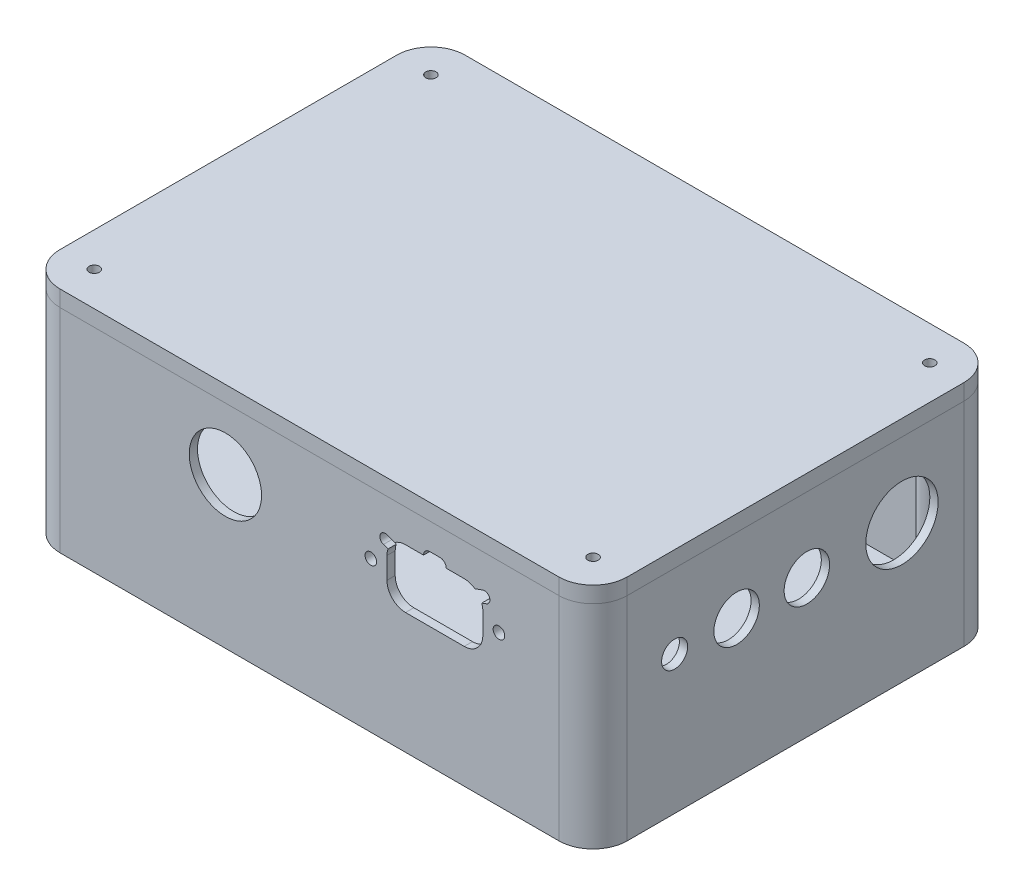
SolidWorks part; units mm, degrees
material "ABS"
ref_plane "Front Plane" through (0, 0, 0) normal (0, 0, 1) x (1, 0, 0)
ref_plane "Top Plane" through (0, 0, 0) normal (0, 1, 0) x (1, 0, 0)
ref_plane "Right Plane" through (0, 0, 0) normal (1, 0, 0) x (0, 0, -1)
sketch "Sketch1" plane through (0, 0, 0) normal (0, 1, 0) x (1, 0, 0)
  line L0 (-76.6347, 59.69) -> (76.6347, 59.69)
  line L1 (-76.6347, 62.23) -> (76.6347, 62.23)
  line L2 (-87.1347, 51.73) -> (-87.1347, -51.73)
  line L3 (-76.6347, -62.23) -> (76.6347, -62.23)
  line L4 (87.1347, 51.73) -> (87.1347, -51.73)
  line L5 (-87.1347, 62.23) -> (87.1347, -62.23) construction
  line L6 (-87.1347, -62.23) -> (87.1347, 62.23) construction
  line L7 (84.5947, 51.73) -> (84.5947, -51.73)
  line L8 (-76.6347, -59.69) -> (76.6347, -59.69)
  line L9 (-84.5947, 51.73) -> (-84.5947, -51.73)
  arc A0 (-87.1347, -51.73) -> (-76.6347, -62.23) centre (-76.6347, -51.73) ccw
  arc A1 (76.6347, -62.23) -> (87.1347, -51.73) centre (76.6347, -51.73) ccw
  arc A2 (76.6347, 62.23) -> (87.1347, 51.73) centre (76.6347, 51.73) cw
  arc A3 (-76.6347, 62.23) -> (-87.1347, 51.73) centre (-76.6347, 51.73) ccw
  arc A4 (76.6347, 59.69) -> (84.5947, 51.73) centre (76.6347, 51.73) cw
  arc A5 (76.6347, -59.69) -> (84.5947, -51.73) centre (76.6347, -51.73) ccw
  arc A6 (-84.5947, -51.73) -> (-76.6347, -59.69) centre (-76.6347, -51.73) ccw
  arc A7 (-76.6347, 59.69) -> (-84.5947, 51.73) centre (-76.6347, 51.73) ccw
  circle A8 centre (-76.6347, 51.73) radius 1.5875
  circle A9 centre (-76.6347, 51.73) radius 2.9845
  circle A10 centre (76.6347, 51.73) radius 1.5875
  circle A11 centre (76.6347, 51.73) radius 2.9845
  circle A12 centre (76.6347, -51.73) radius 1.5875
  circle A13 centre (76.6347, -51.73) radius 2.9845
  circle A14 centre (-76.6347, -51.73) radius 1.5875
  circle A15 centre (-76.6347, -51.73) radius 2.9845
  point P0 (0, 0)
  dimension "D3" = 10.5
  dimension "D5" = 5.969
  dimension "D6" = 3.175
  dimension "D1" = 124.46
  dimension "D2" = 174.2694
  dimension "D4" = 2.54
extrude "Sides" add sketch "Sketch1" along normal blind 60.96 contours L1 A3 L2 A0 L3 A1 L4 A2 A7 L0 A4 L7 A5 L8 A6 L9 | A9 A8 | A11 A10 | A13 A12 | A15 A14
sketch "Sketch2" plane through (0, 0, 0) normal (0, 1, 0) x (1, 0, 0)
  line L4 (-76.6347, -62.23) -> (76.6347, -62.23) construction
  line L5 (87.1347, 51.73) -> (87.1347, -51.73) construction
  line L6 (-76.6347, 62.23) -> (76.6347, 62.23) construction
  line L7 (-87.1347, 51.73) -> (-87.1347, -51.73) construction
  line L8 (-76.6347, -62.23) -> (76.6347, -62.23)
  line L9 (87.1347, 51.73) -> (87.1347, -51.73)
  line L10 (-76.6347, 62.23) -> (76.6347, 62.23)
  line L11 (-87.1347, 51.73) -> (-87.1347, -51.73)
  arc A4 (-87.1347, -51.73) -> (-76.6347, -62.23) centre (-76.6347, -51.73) ccw construction
  arc A5 (76.6347, -62.23) -> (87.1347, -51.73) centre (76.6347, -51.73) ccw construction
  arc A6 (87.1347, 51.73) -> (76.6347, 62.23) centre (76.6347, 51.73) ccw construction
  arc A7 (-76.6347, 62.23) -> (-87.1347, 51.73) centre (-76.6347, 51.73) ccw construction
  arc A8 (-87.1347, -51.73) -> (-76.6347, -62.23) centre (-76.6347, -51.73) ccw
  arc A9 (76.6347, -62.23) -> (87.1347, -51.73) centre (76.6347, -51.73) ccw
  arc A10 (87.1347, 51.73) -> (76.6347, 62.23) centre (76.6347, 51.73) ccw
  arc A11 (-76.6347, 62.23) -> (-87.1347, 51.73) centre (-76.6347, 51.73) ccw
extrude "Bottom" add sketch "Sketch2" against normal blind 4.318
sketch "Sketch3" plane through (0, 60.96, 0) normal (0, 1, 0) x (1, 0, 0)
  line L0 (-87.1347, 51.73) -> (-87.1347, -51.73) construction
  line L1 (-76.6347, 62.23) -> (76.6347, 62.23) construction
  line L2 (87.1347, 51.73) -> (87.1347, -51.73) construction
  line L3 (-76.6347, -62.23) -> (76.6347, -62.23) construction
  line L4 (-87.1347, 51.73) -> (-87.1347, -51.73)
  line L5 (-76.6347, 62.23) -> (76.6347, 62.23)
  line L6 (87.1347, 51.73) -> (87.1347, -51.73)
  line L7 (-76.6347, -62.23) -> (76.6347, -62.23)
  arc A0 (-76.6347, 62.23) -> (-87.1347, 51.73) centre (-76.6347, 51.73) ccw construction
  arc A1 (87.1347, 51.73) -> (76.6347, 62.23) centre (76.6347, 51.73) ccw construction
  arc A2 (76.6347, -62.23) -> (87.1347, -51.73) centre (76.6347, -51.73) ccw construction
  arc A3 (-87.1347, -51.73) -> (-76.6347, -62.23) centre (-76.6347, -51.73) ccw construction
  arc A4 (-76.6347, 62.23) -> (-87.1347, 51.73) centre (-76.6347, 51.73) ccw
  arc A5 (87.1347, 51.73) -> (76.6347, 62.23) centre (76.6347, 51.73) ccw
  arc A6 (76.6347, -62.23) -> (87.1347, -51.73) centre (76.6347, -51.73) ccw
  arc A7 (-87.1347, -51.73) -> (-76.6347, -62.23) centre (-76.6347, -51.73) ccw
  circle A8 centre (76.6347, 51.73) radius 1.5875 construction
  circle A9 centre (76.6347, -51.73) radius 1.5875 construction
  circle A10 centre (-76.6347, -51.73) radius 1.5875 construction
  circle A11 centre (-76.6347, 51.73) radius 1.5875 construction
  circle A12 centre (76.6347, 51.73) radius 1.5875
  circle A13 centre (76.6347, -51.73) radius 1.5875
  circle A14 centre (-76.6347, -51.73) radius 1.5875
  circle A15 centre (-76.6347, 51.73) radius 1.5875
extrude "Lid" add sketch "Sketch3" along normal blind 4.953 separate body
sketch "Sketch4" plane through (-87.1347, 0, 0) normal (-1, 0, 0) x (0, 0, 1)
  line L0 (-51.73, 60.96) -> (51.73, 60.96) construction
  line L3 (7.153, 50.165) -> (34.458, 50.165)
  line L4 (4.613, 47.625) -> (4.613, 28.575)
  line L5 (7.153, 26.035) -> (34.458, 26.035)
  line L6 (36.998, 47.625) -> (36.998, 28.575)
  circle A0 centre (-29.6955, 38.1) radius 11.43
  arc A1 (4.613, 28.575) -> (7.153, 26.035) centre (7.153, 28.575) ccw
  arc A2 (34.458, 26.035) -> (36.998, 28.575) centre (34.458, 28.575) ccw
  arc A3 (34.458, 50.165) -> (36.998, 47.625) centre (34.458, 47.625) cw
  arc A4 (7.153, 50.165) -> (4.613, 47.625) centre (7.153, 47.625) ccw
  point P11 (4.613, 26.035)
  point P16 (36.998, 50.165)
  point P19 (4.613, 50.165)
  point P20 (4.613, 38.1)
  point P21 (20.8055, 50.165)
  dimension "D1" = 22.86
  dimension "D2" = 22.86
  dimension "D3" = 19.05
  dimension "D6" = 2.54
  dimension "D4" = 24.13
  dimension "D5" = 32.385
  dimension "D7" = 27.94
extrude "Power Cuts" cut sketch "Sketch4" against normal up to next (2.54 mm away)
sketch "Sketch5" plane through (0, 0, 62.23) normal (0, 0, 1) x (1, 0, 0)
  line L0 (-76.6347, 60.96) -> (76.6347, 60.96) construction
  line L1 (-76.6347, 60.96) -> (-76.6347, -4.318) construction
  line L2 (76.6347, 60.96) -> (76.6347, -4.318) construction
  circle A0 centre (-25.8347, 41.91) radius 11.1125
  line B0 (18.8497, 41.91) -> (58.2197, 41.91) construction
  line B1 (23.8027, 45.212) -> (23.8027, 38.608)
  line B2 (29.5177, 32.893) -> (47.5517, 32.893)
  line B3 (53.2667, 45.212) -> (53.2667, 38.608)
  circle B4 centre (18.8497, 41.91) radius 1.778
  circle B5 centre (58.2197, 41.91) radius 1.778
  arc B6 (47.5517, 32.893) -> (53.2667, 38.608) centre (47.5517, 38.608) ccw
  arc B7 (23.8027, 38.608) -> (29.5177, 32.893) centre (29.5177, 38.608) ccw
  line B8 (36.9472, 52.832) -> (40.1222, 52.832)
  arc B9 (36.9472, 52.832) -> (35.0422, 50.927) centre (36.9472, 50.927) ccw
  arc B10 (40.1222, 52.832) -> (42.0272, 50.927) centre (40.1222, 50.927) cw
  line B11 (54.3442, 47.6135) -> (52.9399, 47.117)
  arc B12 (53.2435, 50.7267) -> (54.3442, 47.6135) centre (53.7939, 49.1701) cw
  line B13 (50.8488, 49.88) -> (53.2435, 50.7267)
  line B14 (23.8259, 50.7267) -> (26.2206, 49.88)
  arc B15 (22.7252, 47.6135) -> (23.8259, 50.7267) centre (23.2755, 49.1701) cw
  line B16 (24.1295, 47.117) -> (22.7252, 47.6135)
  line B17 (29.5177, 50.927) -> (35.0422, 50.927)
  line B18 (42.0272, 50.927) -> (47.5517, 50.927)
  arc B19 (29.5177, 50.927) -> (26.2206, 49.88) centre (29.5177, 45.212) ccw
  arc B20 (24.1295, 47.117) -> (23.8027, 45.212) centre (29.5177, 45.212) ccw
  arc B21 (47.5517, 50.927) -> (50.8488, 49.88) centre (47.5517, 45.212) cw
  arc B22 (52.9399, 47.117) -> (53.2667, 45.212) centre (47.5517, 45.212) cw
sketch_block_instance "Molex MX150 Panel Mount-1"
sketch_block "Molex MX150 Panel Mount" parameters "D1"=3.556, "D3"=5.715, "D12"=2.2522, "D2"=39.37, "D4"=17.78, "D5"=6.35, "D6"=3.8381, "D7"=3.8381, "D8"=2.0786, "D9"=3.5188, "D10"=3.6262, "D11"=0.691
extrude "Accumulator Cut" cut sketch "Sketch5" against normal up to next (2.54 mm away)
sketch "Sketch6" plane through (87.1347, 0, 0) normal (1, 0, 0) x (0, 0, -1)
  line L0 (51.73, 60.96) -> (-51.73, 60.96) construction
  line L1 (51.73, 60.96) -> (51.73, -4.318) construction
  circle A0 centre (-37.17, 38.1) radius 4.0005
  circle A1 centre (-18.12, 38.1) radius 6.985
  circle A2 centre (3.47, 38.1) radius 6.985
  circle A3 centre (32.68, 38.1) radius 11.1125
  dimension "D1" = 8.001
  dimension "D2" = 13.97
  dimension "D3" = 22.225
  dimension "D4" = 22.86
  dimension "D5" = 19.05
  dimension "D6" = 48.26
  dimension "D7" = 69.85
  dimension "D8" = 88.9
extrude "Panel Cuts" cut sketch "Sketch6" against normal up to next (2.54 mm away)
